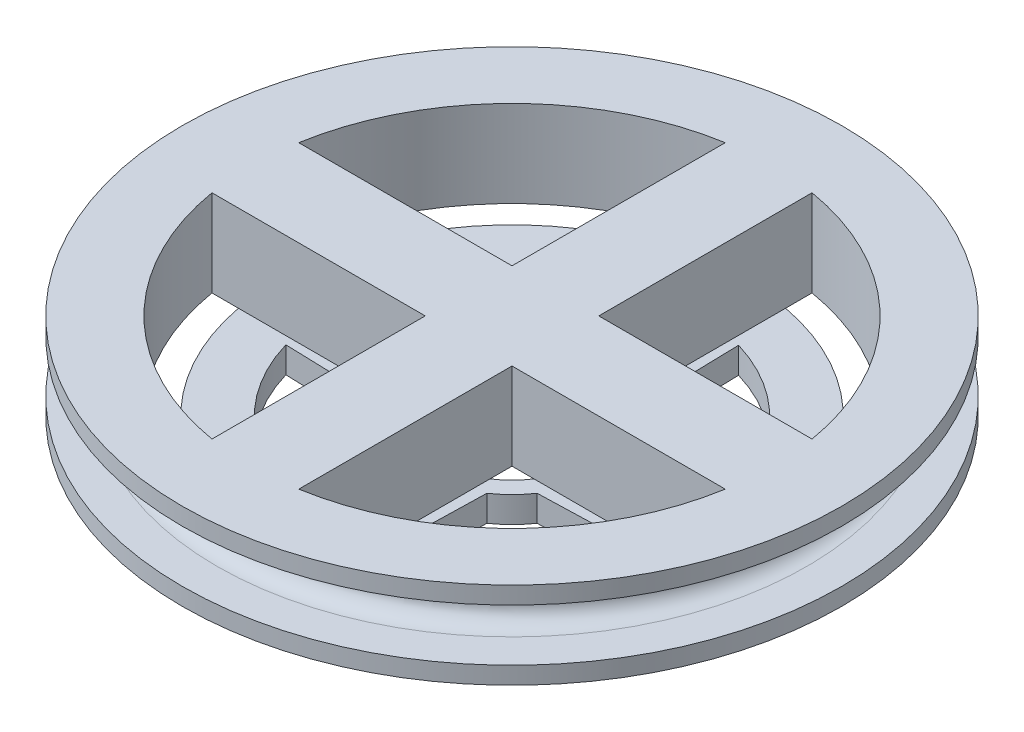
SolidWorks part; units mm, degrees
ref_plane "Front Plane" through (0, 0, 0) normal (0, 0, 1) x (1, 0, 0)
ref_plane "Top Plane" through (0, 0, 0) normal (0, 1, 0) x (1, 0, 0)
ref_plane "Right Plane" through (0, 0, 0) normal (1, 0, 0) x (0, 0, -1)
sketch "Sketch1" plane through (0, 0, 0) normal (0, 1, 0) x (1, 0, 0)
  line L4 (-20, -3.5) -> (-20, 3.5)
  line L5 (-20, 0) -> (-20, -3.5)
  line L6 (-3.5, 20) -> (3.5, 20)
  line L7 (-3.5, 20) -> (-5, 7.5378)
  line L8 (-20, 3.5) -> (-7.5378, 5)
  line L9 (3.5, -20) -> (5, -7.5378)
  line L10 (3.5, 20) -> (5, 7.5378)
  line L11 (-3.5, -20) -> (3.5, -20)
  line L12 (-3.5, -20) -> (-5, -7.5378)
  line L13 (-20, -3.5) -> (-7.5378, -5)
  line L14 (20, -3.5) -> (7.5378, -5)
  line L15 (20, -3.5) -> (20, 3.5)
  line L16 (20, 3.5) -> (7.5378, 5)
  arc A2 (-7.5378, 5) -> (-5, 7.5378) centre (0, 0) cw
  arc A3 (5, 7.5378) -> (7.5378, 5) centre (0, 0) cw
  arc A4 (-5, -7.5378) -> (-7.5378, -5) centre (0, 0) cw
  arc A5 (7.5378, -5) -> (5, -7.5378) centre (0, 0) cw
  circle A6 centre (0, 0) radius 25
extrude "Boss-Extrude2" add sketch "Sketch1" along normal blind 3 contours A6 L14 A5 L9 L11 L12 A4 L13 L4 L8 A2 L7 L6 L10 A3 L16 L15
sketch "Sketch3" plane through (0, 3, 0) normal (0, 1, 0) x (1, 0, 0)
  circle A1 centre (0, 0) radius 38
extrude "Boss-Extrude4" add sketch "Sketch3" along normal blind 2
sketch "Sketch5" plane through (0, 5, 0) normal (0, 1, 0) x (1, 0, 0)
  circle A0 centre (0, 0) radius 32
  circle A1 centre (0, 0) radius 27
extrude "Boss-Extrude5" add sketch "Sketch5" along normal blind 6
sketch "Sketch6" plane through (0, 5, 0) normal (0, 1, 0) x (1, 0, 0)
  circle A0 centre (0, 0) radius 5
extrude "Boss-Extrude7" add sketch "Sketch6" along normal blind 6
sketch "Sketch7" plane through (0, 11, 0) normal (0, 1, 0) x (1, 0, 0)
  circle A1 centre (0, 0) radius 38
extrude "Boss-Extrude9" add sketch "Sketch7" along normal blind 2
fillet "Fillet2" radius 2 1 edges at (0, 11, 32)
fillet "Fillet3" radius 2 1 edges at (0, 5, 32)
fillet "Fillet5" radius 2 1 edges at (0, 3, 25)
sketch "Sketch8" plane through (0, 13, 0) normal (0, 1, 0) x (1, 0, 0)
  circle A0 centre (0, 0) radius 30
extrude "Boss-Extrude10" add sketch "Sketch8" against normal blind 9
sketch "Sketch9" plane through (0, 13, 0) normal (0, 1, 0) x (1, 0, 0)
  line L4 (-5, 30) -> (-5, -30)
  line L5 (5, 30) -> (5, -30)
  line L6 (30, 0) -> (30, -5)
  line L7 (30, -5) -> (5, -5)
  line L8 (30, 5) -> (5, 5)
  line L9 (-30, -5) -> (-5, -5)
  line L10 (-30, 5) -> (-5, 5)
  circle A0 centre (0, 0) radius 30
extrude "Cut-Extrude1" cut sketch "Sketch9" against normal blind 10 contours L5 A0 L7 | L9 A0 L4 | L4 A0 L10 | L8 A0 L5
sketch "Sketch10" plane through (0, 3, 0) normal (0, -1, 0) x (-1, 0, 0)
  line L1 (6.2595, 9.0454) -> (5.9617, 21.0417)
  line L3 (9.0454, 6.2595) -> (21.0396, 5.8876)
  line L4 (-6.2595, -9.0454) -> (-5.9617, -21.0417)
  line L5 (-9.0454, -6.2595) -> (-21.0396, -5.8876)
  line L6 (9.0454, -6.2595) -> (21.0396, -5.8876)
  line L7 (6.2595, -9.0454) -> (5.9617, -21.0417)
  line L8 (-6.2595, 9.0454) -> (-5.9617, 21.0417)
  line L9 (-9.0454, 6.2595) -> (-21.0396, 5.8876)
  circle A0 centre (0, 0) radius 11.0883
  circle A1 centre (0, 0) radius 21
  point P4 (0, 0)
  point P9 (0, 0)
  point P22 (0, 0)
  point P23 (0, 0)
  point P24 (0, 0)
  point P25 (0, 0)
  point P26 (0, 0)
  point P27 (0, 0)
  point P28 (0, 0)
  point P29 (0, 0)
  point P30 (0, 0)
extrude "Cut-Extrude3" cut sketch "Sketch10" along normal blind 10 contours L8 A1 L9 A0 | L3 A1 L1 A0 | L7 A1 L6 A0 | L5 A1 L4 A0
